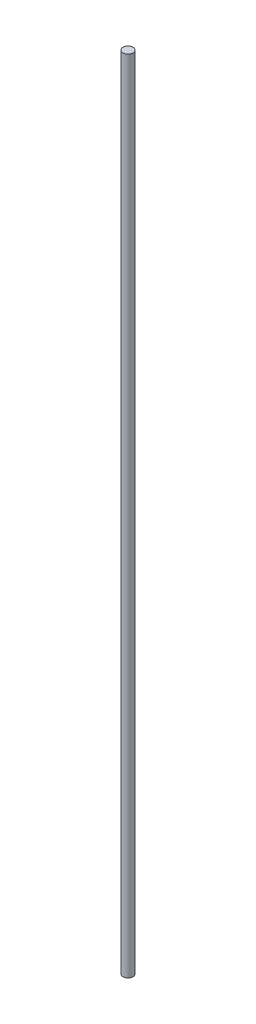
SolidWorks part; units mm, degrees
material "AISI 1020"
ref_plane "Alzado" through (0, 0, 0) normal (0, 0, 1) x (1, 0, 0)
ref_plane "Planta" through (0, 0, 0) normal (0, 1, 0) x (1, 0, 0)
ref_plane "Vista lateral" through (0, 0, 0) normal (1, 0, 0) x (0, 0, -1)
sketch "Croquis1" plane through (0, 0, 0) normal (0, 1, 0) x (1, 0, 0)
  circle A0 centre (0, 0) radius 6.35
  dimension "D1" = 12.7
extrude "Saliente-Extruir1" add sketch "Croquis1" along normal blind 1012
